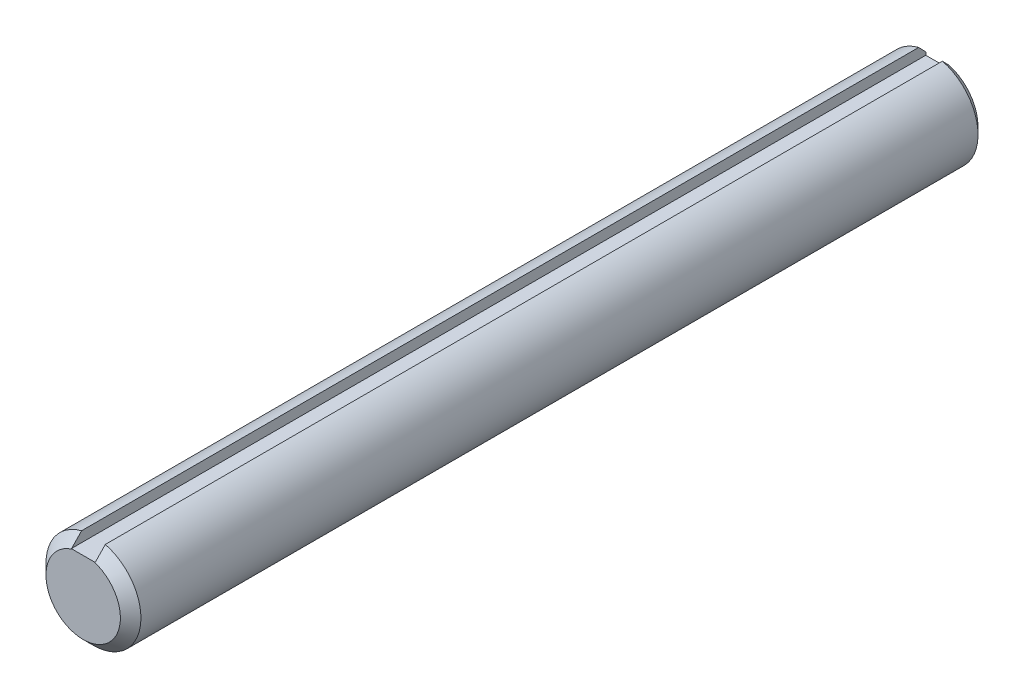
SolidWorks part; units mm, degrees
ref_plane "Front" through (0, 0, 0) normal (0, 0, 1) x (1, 0, 0)
ref_plane "Top" through (0, 0, 0) normal (0, 1, 0) x (1, 0, 0)
ref_plane "Right" through (0, 0, 0) normal (1, 0, 0) x (0, 0, -1)
sketch "Sketch1" plane through (0, 0, 0) normal (0, 0, 1) x (1, 0, 0)
  circle A0 centre (0, 0) radius 6.35
  dimension "dia" = 12.7
extrude "Extrude1" add sketch "Sketch1" along normal mid plane 152.4
sketch "Sketch2" plane through (0, 0, 0) normal (1, 0, 0) x (0, 0, -1)
  point P0 (-76.2, 6.35)
  point P1 (76.2, 6.35)
  point P2 (76.2, -6.35)
chamfer "Chamfer1" distance 0.9525 angle 45 2 edges at (6.35, 0, -76.2) (6.35, 0, 76.2)
sketch "Sketch3" plane through (0, 0, 0) normal (0, 0, 1) x (1, 0, 0)
  line L1 (-1.5875, 6.35) -> (1.5875, 6.35)
  line L2 (-1.5875, 6.35) -> (-1.5875, 4.7625)
  line L3 (-1.5875, 4.7625) -> (1.5875, 4.7625)
  line L4 (1.5875, 6.35) -> (1.5875, 4.7625)
  dimension "key wd" = 3.175
  dimension "key dp" = 1.5875
extrude "Extrude2" cut sketch "Sketch3" against normal through all and the other way through all
ref_plane "Plane1" through (0, 0, 38.1) normal (0, 0, 1) x (1, 0, 0)
other "SurfaceCut1"
chamfer "Chamfer2" distance 1.3735 angle 45 1 edges at (0, -6.35, 38.1)
equation "\"D1@Chamfer1\" = \"dia@Sketch1\" * .075"
